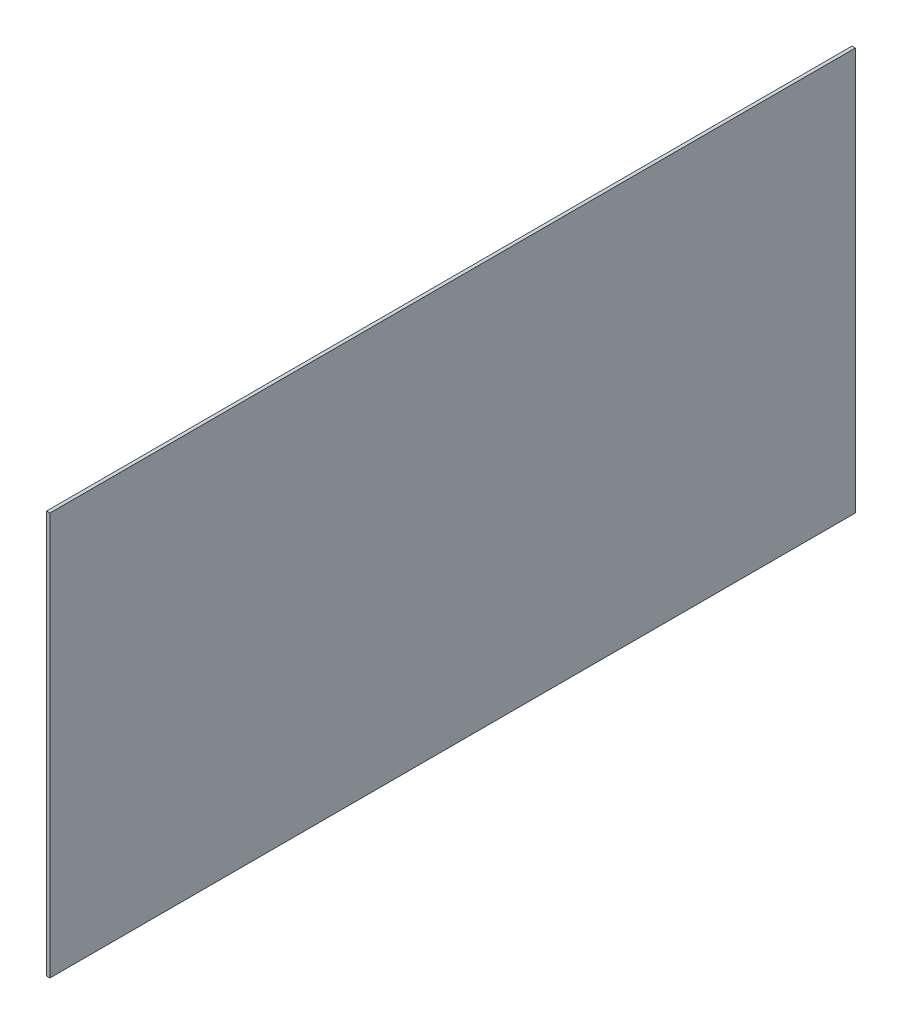
SolidWorks part; units mm, degrees
ref_plane "Front Plane" through (0, 0, 0) normal (0, 0, 1) x (1, 0, 0)
ref_plane "Top Plane" through (0, 0, 0) normal (0, 1, 0) x (1, 0, 0)
ref_plane "Right Plane" through (0, 0, 0) normal (1, 0, 0) x (0, 0, -1)
sketch "Sketch1" plane through (0, 0, 0) normal (1, 0, 0) x (0, 0, -1)
  line L1 (-304.8, 152.4) -> (304.8, 152.4)
  line L2 (-304.8, 152.4) -> (-304.8, -152.4)
  line L3 (-304.8, -152.4) -> (304.8, -152.4)
  line L4 (304.8, 152.4) -> (304.8, -152.4)
  line L5 (-304.8, 152.4) -> (304.8, -152.4) construction
  line L6 (-304.8, -152.4) -> (304.8, 152.4) construction
  point P0 (0, 0)
  dimension "D1" = 609.6
  dimension "D2" = 304.8
extrude "Boss-Extrude1" add sketch "Sketch1" along normal blind 2.54
